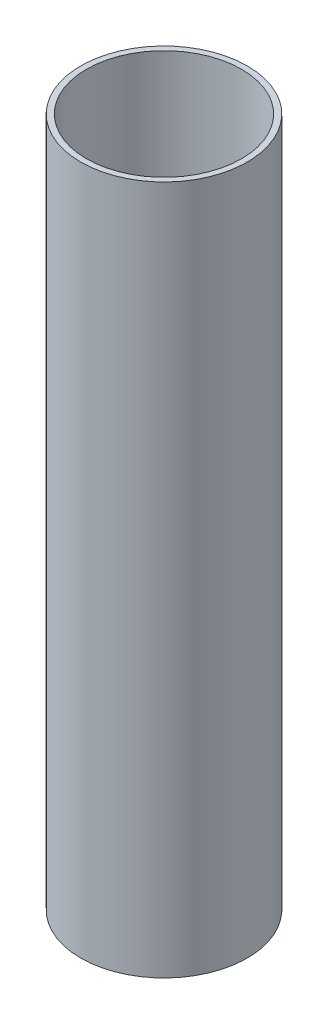
SolidWorks part; units mm, degrees
material "C-Glass Fiber"
ref_plane "Front Plane" through (0, 0, 0) normal (0, 0, 1) x (1, 0, 0)
ref_plane "Top Plane" through (0, 0, 0) normal (0, 1, 0) x (1, 0, 0)
ref_plane "Right Plane" through (0, 0, 0) normal (1, 0, 0) x (0, 0, -1)
sketch "Sketch1" plane through (0, 0, 0) normal (0, 1, 0) x (1, 0, 0)
  circle A0 centre (0, 0) radius 27
  circle A1 centre (0, 0) radius 29
  dimension "D1" = 54
  dimension "D2" = 58
extrude "Boss-Extrude1" add sketch "Sketch1" along normal blind 240
